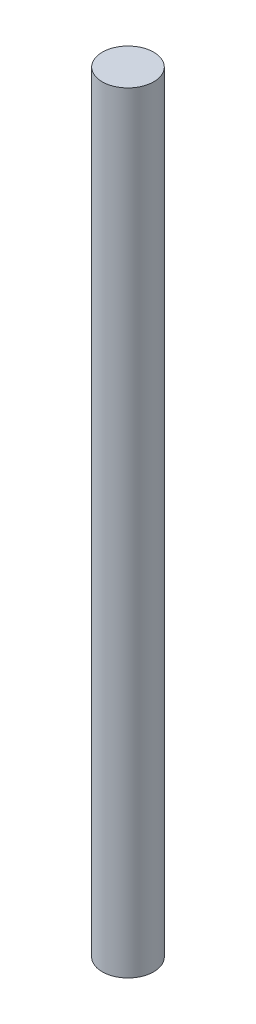
SolidWorks part; units mm, degrees
ref_plane "Front Plane" through (0, 0, 0) normal (0, 0, 1) x (1, 0, 0)
ref_plane "Top Plane" through (0, 0, 0) normal (0, 1, 0) x (1, 0, 0)
ref_plane "Right Plane" through (0, 0, 0) normal (1, 0, 0) x (0, 0, -1)
sketch "Sketch1" plane through (0, 0, 0) normal (0, 1, 0) x (1, 0, 0)
  circle A0 centre (0, 0) radius 5
  dimension "D1" = 10
extrude "Boss-Extrude1" add sketch "Sketch1" along normal blind 150 contours A0
